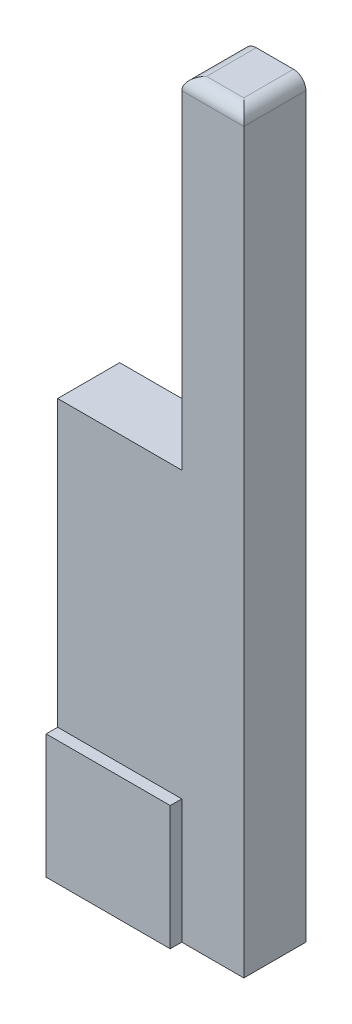
SolidWorks part; units mm, degrees
ref_plane "Front Plane" through (0, 0, 0) normal (0, 0, 1) x (1, 0, 0)
ref_plane "Top Plane" through (0, 0, 0) normal (0, 1, 0) x (1, 0, 0)
ref_plane "Right Plane" through (0, 0, 0) normal (1, 0, 0) x (0, 0, -1)
sketch "Sketch1" plane through (0, 0, 0) normal (0, 0, 1) x (1, 0, 0)
  line L0 (73.1733, 0) -> (-83.3727, 0) construction
  line L1 (10, 12) -> (10, -15.48)
  line L2 (0, 0) -> (10, 0) construction
  line L3 (0, 0) -> (0, -15.48) construction
  line L4 (0, -15.48) -> (10, -15.48) construction
  line L5 (10, 0) -> (10, -15.48) construction
  line L6 (10, -15.48) -> (0, -15.48)
  line L7 (0, -15.48) -> (0, -48.42)
  line L8 (0, -48.42) -> (15, -48.42)
  line L9 (-83.3727, -7.64) -> (73.1733, -7.64) construction
  line L10 (-83.3727, -48.42) -> (73.1733, -48.42) construction
  line L11 (15, -48.42) -> (15, 12)
  line L12 (15, 12) -> (10, 12)
  line L13 (0, -43.42) -> (15, -43.42) construction
  dimension "D1" = 10
  dimension "D2" = 15.48
  dimension "D3" = 5
  dimension "D4" = 12
  dimension "D5" = 7.64
  dimension "D6" = 40.78
  dimension "D7" = 0
  dimension "D8" = 5
extrude "Boss-Extrude1" add sketch "Sketch1" along normal blind 5
sketch "Sketch2" plane through (0, 0, 0) normal (0, 0, -1) x (-1, 0, 0)
  line L0 (0, -43.42) -> (-10, -43.42) construction
  line L1 (0, -38.42) -> (-10, -38.42)
  line L2 (0, -38.42) -> (0, -48.42)
  line L3 (0, -48.42) -> (-10, -48.42)
  line L4 (-10, -38.42) -> (-10, -48.42)
  line L5 (0, -48.42) -> (-15, -48.42) construction
  line L6 (-10, -15.48) -> (0, -15.48) construction
  line L7 (-5, -31.4048) -> (-5, -38.42) construction
  line L8 (0, -15.48) -> (0, -48.42) construction
  point P13 (-5, -38.42)
  dimension "D1" = 5
  dimension "D2" = 10
  dimension "D3" = 10
extrude "Boss-Extrude2" add sketch "Sketch2" against normal blind 5.93
fillet "Fillet1" radius 1 3 edges at (10, 12, 2.5) (15, 12, 2.5) (12.5, 12, 5)
sketch "Sketch3" plane through (0, -48.42, 0) normal (0, -1, 0) x (1, 0, 0)
  line L0 (15, 2.5) -> (0, 2.5) construction
  line L1 (15, 5) -> (15, 0) construction
  circle A0 centre (12.5, 2.5) radius 1.0294
  dimension "D1" = 2.5
extrude "Cut-Extrude1" cut sketch "Sketch3" against normal blind 0.5
